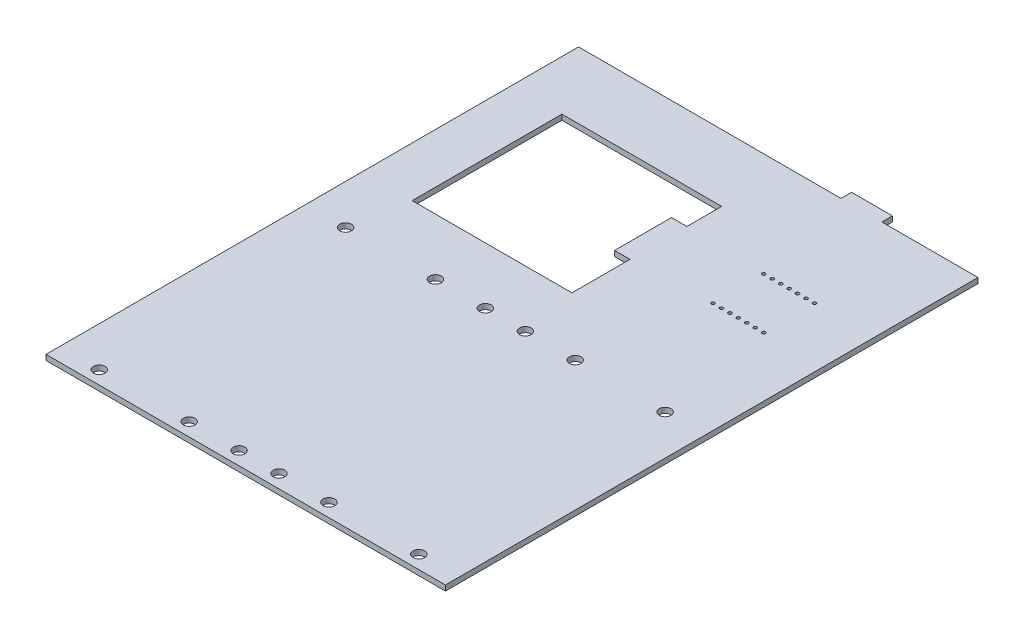
SolidWorks part; units mm, degrees
ref_plane "Front Plane" through (0, 0, 0) normal (0, 0, 1) x (1, 0, 0)
ref_plane "Top Plane" through (0, 0, 0) normal (0, 1, 0) x (1, 0, 0)
ref_plane "Right Plane" through (0, 0, 0) normal (1, 0, 0) x (0, 0, -1)
sketch "Sketch1" plane through (0, 0, 0) normal (0, 1, 0) x (1, 0, 0)
  line L0 (84.17, -43.34) -> (83.15, -43.34)
  line L1 (0, 0) -> (120, 0)
  line L2 (0, 0) -> (0, -160)
  line L3 (0, -160) -> (120, -160)
  line L4 (120, 0) -> (120, -160)
  line L9 (105, -47.78) -> (84.17, -47.78)
  line L10 (105, -47.78) -> (105, -30)
  line L12 (8, -78) -> (58, -78)
  line L13 (8, -78) -> (8, -160)
  line L14 (8, -160) -> (58, -160)
  line L15 (58, -78) -> (58, -160)
  line L16 (62, -78) -> (112, -78)
  line L17 (62, -78) -> (62, -160)
  line L18 (62, -160) -> (112, -160)
  line L19 (112, -78) -> (112, -160)
  line L24 (63, -65) -> (15, -65)
  line L25 (63, -65) -> (63, -20)
  line L26 (18.43, -160) -> (18.43, -166.096)
  line L27 (18.43, -166.096) -> (48.43, -166.096)
  line L28 (48.43, -166.096) -> (48.43, -160)
  line L43 (60, -78) -> (60, -160) construction
  line L44 (101.57, -160) -> (101.57, -166.096)
  line L45 (101.57, -166.096) -> (71.57, -166.096)
  line L46 (71.57, -166.096) -> (71.57, -160)
  line L50 (105, -30) -> (84.17, -30)
  line L51 (84.17, -47.78) -> (84.17, -30)
  line L52 (83.15, -43.34) -> (83.15, -34.45)
  line L53 (83.15, -34.45) -> (84.17, -34.45)
  line L54 (63, -20) -> (15, -20)
  line L55 (15, -65) -> (15, -20)
  line L56 (85, -160) -> (35, -160)
  line L57 (85, -160) -> (85, -78)
  line L58 (85, -78) -> (35, -78)
  line L59 (35, -160) -> (35, -78)
  line L60 (72.622, -47.55) -> (58.372, -47.55)
  line L61 (72.622, -47.55) -> (72.622, -30.45)
  line L62 (72.622, -30.45) -> (58.372, -30.45)
  line L63 (58.372, -47.55) -> (58.372, -30.45)
  line L64 (91.12, -13.104) -> (78.84, -13.104)
  line L65 (91.12, -13.104) -> (91.12, 3.176)
  line L66 (91.12, 3.176) -> (78.84, 3.176)
  line L67 (78.84, -13.104) -> (78.84, 3.176)
  circle A4 centre (12, -82) radius 1.75
  circle A5 centre (54, -82) radius 1.75
  circle A6 centre (12, -156) radius 1.75
  circle A7 centre (54, -156) radius 1.75
  circle A8 centre (66, -82) radius 1.75
  circle A9 centre (108, -82) radius 1.75
  circle A10 centre (66, -156) radius 1.75
  circle A11 centre (108, -156) radius 1.75
  circle A80 centre (81, -156) radius 1.75
  circle A81 centre (39, -156) radius 1.75
  circle A82 centre (39, -82) radius 1.75
  circle A83 centre (81, -82) radius 1.75
  circle A84 centre (86.9, -46.51) radius 0.5
  circle A85 centre (89.44, -46.51) radius 0.5
  circle A86 centre (91.98, -46.51) radius 0.5
  circle A87 centre (94.52, -46.51) radius 0.5
  circle A88 centre (97.06, -46.51) radius 0.5
  circle A89 centre (99.6, -46.51) radius 0.5
  circle A90 centre (102.14, -46.51) radius 0.5
  circle A91 centre (89.44, -31.27) radius 0.5
  circle A92 centre (91.98, -31.27) radius 0.5
  circle A93 centre (94.52, -31.27) radius 0.5
  circle A94 centre (97.06, -31.27) radius 0.5
  circle A95 centre (99.6, -31.27) radius 0.5
  circle A96 centre (102.14, -31.27) radius 0.5
  circle A97 centre (86.9, -31.27) radius 0.5
  dimension "D11" = 3.5
  dimension "D27" = 3.5
  dimension "D33" = 1
  dimension "D1" = 120
  dimension "D2" = 160
  dimension "D3" = 42
  dimension "D4" = 42
  dimension "D5" = 74
  dimension "D6" = 12
  dimension "D7" = 12
  dimension "D19" = 82
  dimension "D20" = 50
  dimension "D21" = 4
  dimension "D22" = 4
  dimension "D23" = 4
  dimension "D24" = 4
  dimension "D30" = 30
  dimension "D31" = 6.096
  dimension "D32" = 9.57
  dimension "D37" = 2
  dimension "D8" = 20.83
  dimension "D9" = 17.78
  dimension "D10" = 8.89
  dimension "D12" = 1.02
  dimension "4.45" = 4.45
  dimension "D13" = 15
  dimension "D14" = 30
  dimension "D15" = 45
  dimension "D17" = 48
  dimension "D25" = 50
  dimension "D26" = 35
  dimension "D28" = 4
  dimension "D29" = 4
  dimension "D34" = 2.73
  dimension "D35" = 1.27
  dimension "D39" = 2.54
  dimension "D40" = 2.73
  dimension "D41" = 1.27
  dimension "D42" = 112.45
  dimension "D43" = 47.378
  dimension "D44" = 14.25
  dimension "D45" = 17.1
  dimension "D16" = 95
  dimension "D18" = 57
  dimension "D46" = 28.88
  dimension "D47" = 146.896
  dimension "D48" = 16.28
  dimension "D49" = 12.28
  dimension "D36" = 7
  dimension "D38" = 2
extrude "Boss-Extrude2" add sketch "Sketch1" along normal blind 1.6 contours L58 L16 L19 L3 L4 L1 L2 L13 L12 L52 L53 L51 L50 L10 L9 L0 L24 L55 L54 L25 | L57 L3 L18 L19 L16 A11 A9 | L14 L59 L12 L13 L3 A6 A4 | L59 L3 L15 L12 A82 A81 A7 A5 | L18 L57 L16 L17 L3 A83 A80 A10 A8 | L58 L43 L56 L17 | L43 L58 L15 L3 | L51 L9 L10 L50 | L53 L52 L0 L51 | L61 L62 L25 L60 | L63 L60 L25 L62 | L67 L64 L65 L1 | L67 L1 L65 L66
equation "\"D4@Sketch1\"=\"D3@Sketch1\""
equation "\"D24@Sketch1\"=\"D22@Sketch1\""
equation "\"D23@Sketch1\"=\"D22@Sketch1\""
equation "\"D25@Sketch1\"=\"D20@Sketch1\""
equation "\"D26@Sketch1\"=(\"D1@Sketch1\"-\"D25@Sketch1\")/2"
equation "\"D27@Sketch1\"=\"D11@Sketch1\""
equation "\"D28@Sketch1\"=\"D24@Sketch1\""
equation "\"D29@Sketch1\"=\"D22@Sketch1\""
equation "\"D41@Sketch1\"=\"D35@Sketch1\""
equation "\"D40@Sketch1\"=\"D34@Sketch1\""
